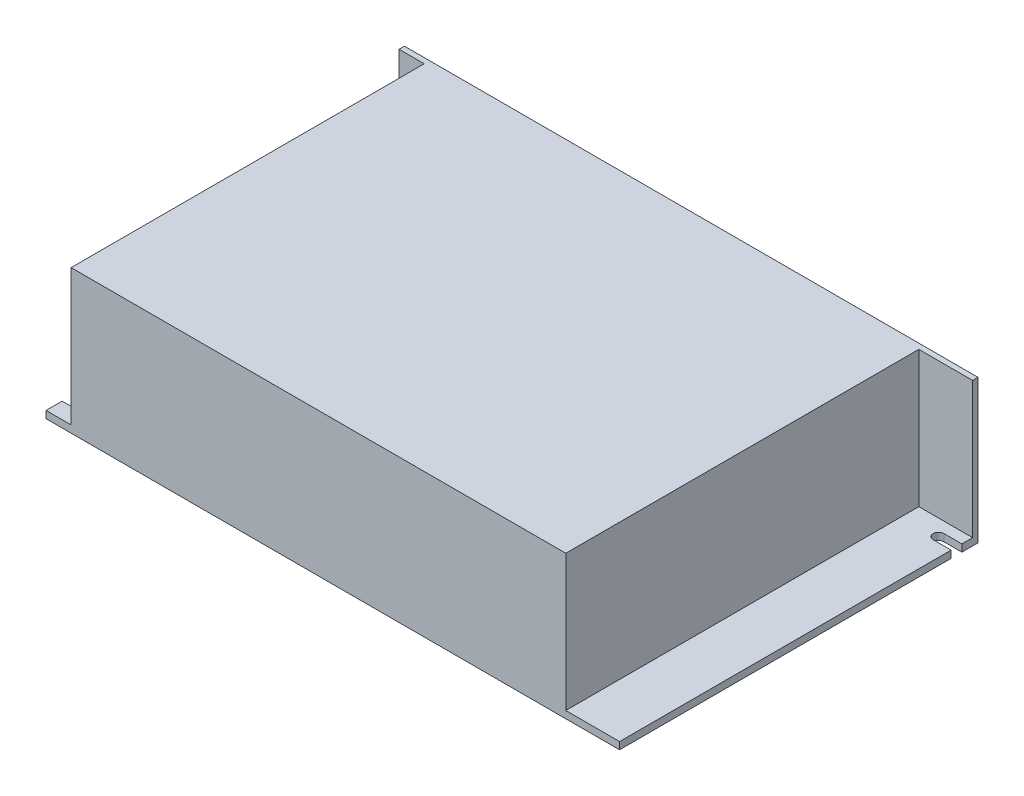
SolidWorks part; units mm, degrees
ref_plane "Front Plane" through (0, 0, 0) normal (0, 0, 1) x (1, 0, 0)
ref_plane "Top Plane" through (0, 0, 0) normal (0, 1, 0) x (1, 0, 0)
ref_plane "Right Plane" through (0, 0, 0) normal (1, 0, 0) x (0, 0, -1)
sketch "Sketch1" plane through (0, 0, 0) normal (0, 0, 1) x (1, 0, 0)
  line L1 (-80, -20) -> (80, -20)
  line L2 (-80, -20) -> (-80, 20)
  line L3 (-80, 20) -> (80, 20)
  line L4 (80, -20) -> (80, 20)
  line L5 (-80, -20) -> (80, 20) construction
  line L6 (-80, 20) -> (80, -20) construction
  point P0 (0, 0)
  dimension "D1" = 40
  dimension "D2" = 160
extrude "Boss-Extrude1" add sketch "Sketch1" along normal blind 100
sketch "Sketch2" plane through (0, 20, 0) normal (0, 1, 0) x (1, 0, 0)
  line L0 (-80, -100) -> (-80, 0) construction
  line L1 (-80, -1.5) -> (-73, -1.5)
  line L2 (-80, -1.5) -> (-80, -100)
  line L3 (-80, -100) -> (-73, -100)
  line L4 (-73, -1.5) -> (-73, -100)
  line L5 (80, -100) -> (-80, -100) construction
  line L6 (80, -100) -> (80, 0) construction
  line L7 (80, -1.5) -> (65, -1.5)
  line L8 (80, -1.5) -> (80, -100)
  line L9 (80, -100) -> (65, -100)
  line L10 (65, -1.5) -> (65, -100)
  line L11 (80, 0) -> (-80, 0) construction
  dimension "D1" = 15
  dimension "D2" = 1.5
  dimension "D3" = 1.5
  dimension "D4" = 7
extrude "Cut-Extrude1" cut sketch "Sketch2" against normal offset from surface (38 mm away) 2 up to face at (0, -20, 50)
sketch "Sketch3" plane through (0, -18, 0) normal (0, 1, 0) x (1, 0, 0)
  line L0 (80, -4.5) -> (75, -4.5)
  line L1 (80, -1.5) -> (80, -100) construction
  line L2 (75, -7.5) -> (80, -7.5)
  line L3 (80, -4.5) -> (80, -7.5)
  line L4 (-80, -92.5) -> (-75, -92.5)
  line L5 (-80, -100) -> (-80, -1.5) construction
  line L6 (-75, -95.5) -> (-80, -95.5)
  line L7 (-80, -95.5) -> (-80, -92.5)
  line L8 (80, 0) -> (-80, 0) construction
  line L9 (-73, -100) -> (-80, -100) construction
  arc A0 (75, -4.5) -> (75, -7.5) centre (75, -6) ccw
  arc A1 (-75, -92.5) -> (-75, -95.5) centre (-75, -94) cw
  dimension "D1" = 3
  dimension "D2" = 3
  dimension "D3" = 5
  dimension "D4" = 5
  dimension "D5" = 6
  dimension "D6" = 6
extrude "Cut-Extrude2" cut sketch "Sketch3" against normal blind 2
